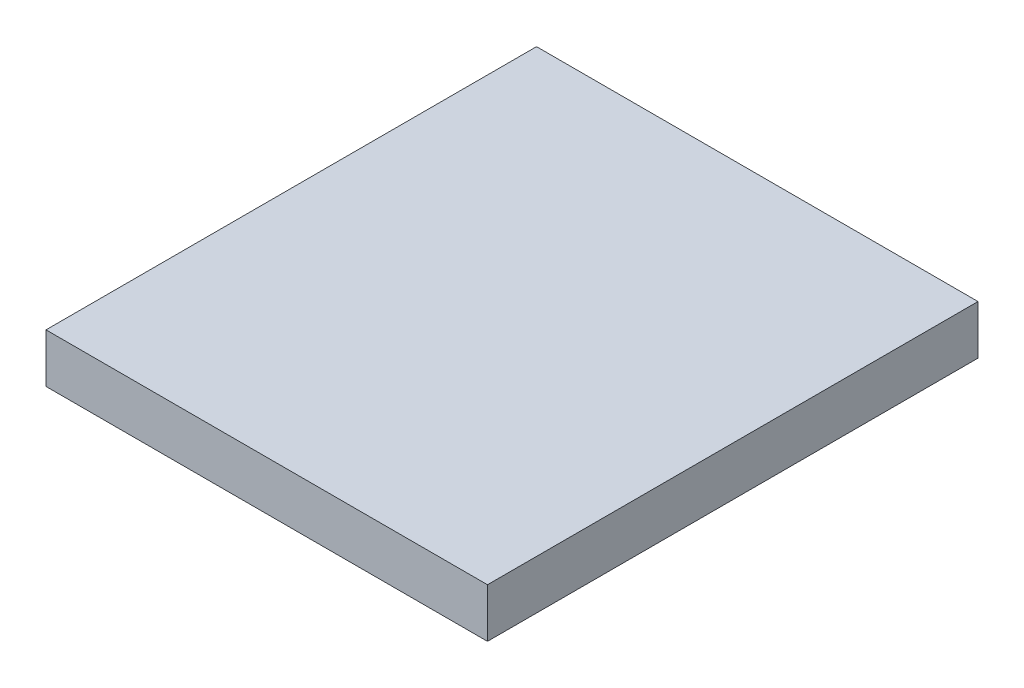
SolidWorks part; units mm, degrees
ref_plane "Front Plane" through (0, 0, 0) normal (0, 0, 1) x (1, 0, 0)
ref_plane "Top Plane" through (0, 0, 0) normal (0, 1, 0) x (1, 0, 0)
ref_plane "Right Plane" through (0, 0, 0) normal (1, 0, 0) x (0, 0, -1)
sketch "Sketch1" plane through (0, 0, 0) normal (0, 1, 0) x (1, 0, 0)
  line L1 (-9, 10) -> (9, 10)
  line L2 (-9, 10) -> (-9, -10)
  line L3 (-9, -10) -> (9, -10)
  line L4 (9, 10) -> (9, -10)
  line L5 (-9, 10) -> (9, -10) construction
  line L6 (-9, -10) -> (9, 10) construction
  point P0 (0, 0)
  dimension "D1" = 20
  dimension "D2" = 18
extrude "Boss-Extrude1" add sketch "Sketch1" along normal blind 2
